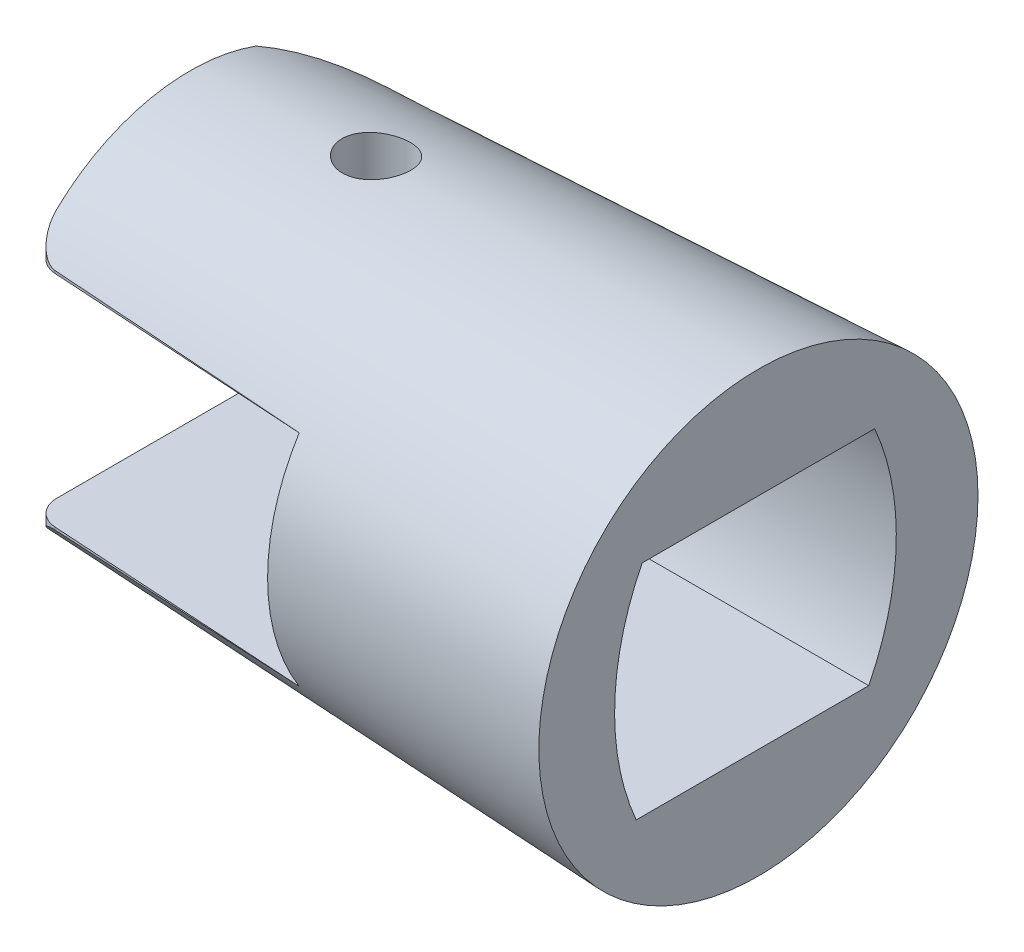
SolidWorks part; units mm, degrees
material "1060 Alloy"
ref_plane "Front Plane" through (0, 0, 0) normal (0, 0, 1) x (1, 0, 0)
ref_plane "Top Plane" through (0, 0, 0) normal (0, 1, 0) x (1, 0, 0)
ref_plane "Right Plane" through (0, 0, 0) normal (1, 0, 0) x (0, 0, -1)
sketch "Sketch1" plane through (0, 0, 0) normal (0, 1, 0) x (1, 0, 0)
  line L0 (0, 0) -> (-22, 0)
  dimension "D1" = 22
ref_plane "Plane1" through (-22, 0, 0) normal (1, 0, 0) x (0, 0, -1)
sketch "Sketch2" plane through (-22, 0, 0) normal (1, 0, 0) x (0, 0, -1)
  circle A0 centre (0, 0) radius 7.5
  dimension "D1" = 15
sketch "Sketch3" plane through (0, 0, 0) normal (1, 0, 0) x (0, 0, -1)
  circle A0 centre (0, 0) radius 8.5
  dimension "D1" = 17
loft "Loft1" add profiles "Sketch3", "Sketch2"
sketch "Sketch4" plane through (0, 0, 0) normal (0, 0, 1) x (1, 0, 0)
  line L0 (0, 0) -> (-10, 0) construction
  line L1 (-24.98, 4.25) -> (-11, 4.25)
  line L2 (-24.98, 4.25) -> (-24.98, -4.25)
  line L3 (-24.98, -4.25) -> (-11, -4.25)
  line L4 (-11, 4.25) -> (-11, -4.25)
  line L5 (0, 0) -> (-22, 0) construction
  dimension "D1" = 10
  dimension "D2" = 11
  dimension "D3" = 8.5
  dimension "D4" = 4.25
  dimension "D5" = 24.98
extrude "Cut-Extrude1" cut sketch "Sketch4" against normal mid plane 20
sketch "Sketch5" plane through (0, 0, 0) normal (0, 1, 0) x (1, 0, 0)
  line L0 (-11, 10.1467) -> (-11, 6.7777)
  line L1 (-27.92, 10.1467) -> (-11, 10.1467)
  line L2 (-27.92, 10.1467) -> (-27.92, -8.7233)
  line L3 (-27.92, -8.7233) -> (-11, -8.7233)
  line L5 (-11, -8.7233) -> (-11, -6.7777)
  line L6 (-11, -6.7777) -> (-23, -6.0438)
  line L7 (-23, -6.0438) -> (-23.0248, -1.4938)
  line L8 (-11, 6.7777) -> (-16.53, 6.6851)
  line L9 (-11, 6.7777) -> (-11, -6.7777)
  arc A0 (-23.0248, -1.4938) -> (-16.53, 6.6851) centre (-14.685, -1.4483) cw
  dimension "D4" = 8.34
  dimension "D1" = 4.55
  dimension "D2" = 12
  dimension "D3" = 5.53
  dimension "D5" = 86.5
  dimension "D6" = 27.92
  dimension "D7" = 18.87
  dimension "D8" = 89.04
extrude "Cut-Extrude2" cut sketch "Sketch5" against normal mid plane 20 contours L7 A0 L8 L0 L1 L2 L3 L5 L6
sketch "Sketch6" plane through (0, 0, 0) normal (0, 1, 0) x (1, 0, 0)
  line L0 (-15.3, 0.5) -> (-15.3, -8) construction
  line L1 (-15.3, -8) -> (-11, -8) construction
  circle A0 centre (-15.3, 0.5) radius 1.25
  dimension "D3" = 2.5
  dimension "D1" = 8.5
  dimension "D2" = 4.3
extrude "Cut-Extrude3" cut sketch "Sketch6" against normal mid plane 20
sketch "Sketch7" plane through (0, 0, 0) normal (1, 0, 0) x (0, 0, -1)
  line L0 (-3.48, 3.3152) -> (-3.48, -5.2448)
  line L1 (5.15, 3.6321) -> (5.15, -4.7879)
  line L2 (0, 8.5) -> (0, -8.5) construction
  arc A0 (-3.48, 3.3152) -> (5.15, 3.6321) centre (1.1838, -6.0252) cw
  arc A1 (-3.48, -5.2448) -> (5.15, -4.7879) centre (0.3925, 3.3424) ccw
  circle A2 centre (0, 0) radius 8.5 construction
  dimension "D1" = 10.44
  dimension "D2" = 9.42
  dimension "D3" = 8.56
  dimension "D4" = 8.42
  dimension "D5" = 8.63
  dimension "D6" = 3.48
sketch "Sketch8" plane through (0, 0, 0) normal (1, 0, 0) x (0, 0, -1)
  line L0 (-8.5, 0) -> (8.5, 0) construction
  line L1 (0, 8.5) -> (0, -8.5) construction
  line L2 (-4.5, 4.25) -> (4.5, 4.25)
  line L3 (-4.73, -4.25) -> (4.27, -4.25)
  circle A0 centre (0, 0) radius 8.5 construction
  arc A1 (-4.5, 4.25) -> (-4.73, -4.25) centre (4.4329, -0.2448) ccw
  arc A2 (4.5, 4.25) -> (4.27, -4.25) centre (-4.6629, 0.2448) cw
  dimension "D2" = 10
  dimension "D1" = 9
  dimension "D3" = 4.25
  dimension "D4" = 8.5
  dimension "D5" = 4.5
  dimension "D6" = 4.73
extrude "Cut-Extrude4" cut sketch "Sketch8" against normal blind 12
fillet "Fillet1" radius 1 2 edges
